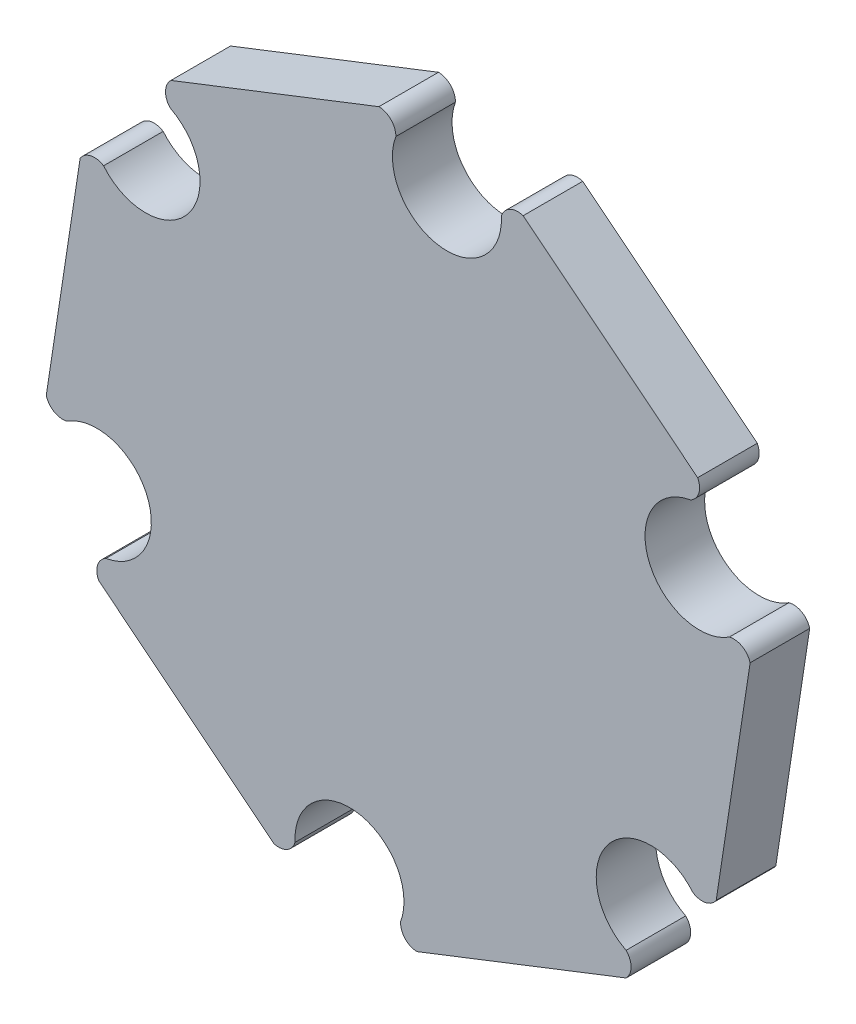
SolidWorks part; units mm, degrees
material "1060 slitina"
ref_plane "Přední rovina" through (0, 0, 0) normal (0, 0, 1) x (1, 0, 0)
ref_plane "Horní rovina" through (0, 0, 0) normal (0, 1, 0) x (1, 0, 0)
ref_plane "Pravá rovina" through (0, 0, 0) normal (1, 0, 0) x (0, 0, -1)
sketch "Skica1" plane through (0, 0, 0) normal (0, 0, 1) x (1, 0, 0)
  line L1 (-5.3857, 0.2391) -> (-4.3897, 6.7784)
  line L2 (-5.9299, 10.7161) -> (-11.0543, 14.8156)
  line L3 (-21.3984, 13.0839) -> (-15.2896, 15.4706)
  line L4 (-24.0633, 9.7716) -> (-25.0577, 3.243)
  line L5 (-23.518, -0.6978) -> (-18.3711, -4.8153)
  line L6 (-14.1786, -5.4602) -> (-8.0304, -3.0582)
  line L12 (-12.994, 16.3674) -> (-23.6955, 12.1864) [skipped]
  line L23 (-6.4189, 0.3965) -> (-6.3928, 0.3925)
  arc A2 (-14.7931, 14.9589) -> (-11.6959, 14.4872) centre (-13.2935, 14.4008) ccw
  arc A3 (-6.1418, 10.0439) -> (-5.0017, 7.1258) centre (-5.8753, 8.4662) ccw
  arc A4 (-23.3752, 9.9241) -> (-21.4181, 12.3705) centre (-22.1422, 10.9437) ccw
  arc A5 (-6.0709, 0.0971) -> (-8.0323, -2.3546) centre (-7.3057, -0.9255) ccw
  arc A6 (-14.6548, -4.9406) -> (-17.752, -4.4689) centre (-16.1543, -4.3826) ccw
  arc A7 (-23.3061, -0.0256) -> (-24.4462, 2.8925) centre (-23.5726, 1.552) ccw
  arc A8 (-11.6959, 14.4872) -> (-11.0543, 14.8156) centre (-11.2109, 14.3306) cw
  arc A9 (-5.9299, 10.7161) -> (-6.1418, 10.0439) centre (-6.3719, 10.4859) cw
  arc A10 (-5.0017, 7.1258) -> (-4.3897, 6.7784) centre (-4.8699, 6.6451) cw
  arc A11 (-15.2896, 15.4706) -> (-14.7931, 14.9589) centre (-15.2972, 14.9665) cw
  arc A12 (-21.4181, 12.3705) -> (-21.3984, 13.0839) centre (-21.0516, 12.7173) cw
  arc A13 (-24.0633, 9.7716) -> (-23.3752, 9.9241) centre (-23.643, 9.5038) cw
  arc A14 (-5.3857, 0.2391) -> (-6.0709, 0.0971) centre (-5.7993, 0.5107) cw
  arc A15 (-8.0323, -2.3546) -> (-8.0304, -3.0582) centre (-8.3831, -2.7073) cw
  arc A16 (-14.1786, -5.4602) -> (-14.6548, -4.9406) centre (-14.1569, -4.9623) cw
  arc A17 (-17.752, -4.4689) -> (-18.3711, -4.8153) centre (-18.2348, -4.3326) cw
  arc A18 (-24.4462, 2.8925) -> (-25.0577, 3.243) centre (-24.5767, 3.3735) cw
  arc A19 (-23.518, -0.6978) -> (-23.3061, -0.0256) centre (-23.076, -0.4677) cw
extrude "Přidat vysunutím1" add sketch "Skica1" along normal blind 1.75 contours A19 L5 A17 A6 A16 L6 A15 A5 A14 L1 A10 A3 A9 L2 A8 A2 A11 L3 A12 A4 A13 L4 A18 A7
ref_plane "Rovina1" through (0, 0, 1.75) normal (0, 0, 1) x (1, 0, 0)
sketch "Skica2" plane through (0, 0, 1.75) normal (0, 0, 1) x (1, 0, 0)
  line L0 (-20.8928, 9.9442) -> (-8.5576, 0.0761) construction
  line L1 (-8.4921, 12.7659) -> (-20.9446, -2.7566) construction
  line L2 (-5.9299, 10.7161) -> (-11.0543, 14.8156) construction
  line L3 (-23.518, -0.6978) -> (-18.3711, -4.8153) construction
  line L4 (-18.344, 14.2772) -> (-11.1045, -4.2592) construction
  line L5 (-21.3984, 13.0839) -> (-15.2896, 15.4706) construction
  line L6 (-14.1786, -5.4602) -> (-8.0304, -3.0582) construction
  line L7 (-13.5345, 12.8191) -> (-15.9134, -2.8008) construction
  arc A0 (-23.3752, 9.9241) -> (-21.4181, 12.3705) centre (-22.1422, 10.9437) ccw construction
  arc A1 (-6.0709, 0.0971) -> (-8.0323, -2.3546) centre (-7.3057, -0.9255) ccw construction
  arc A2 (-14.7931, 14.9589) -> (-11.6959, 14.4872) centre (-13.2935, 14.4008) ccw construction
  arc A3 (-14.6548, -4.9406) -> (-17.752, -4.4689) centre (-16.1543, -4.3826) ccw construction
  point P28 (-14.7252, 5.0101)
ref_plane "Rovina2" through (0, 0, 0) normal (0, 0, -1) x (-1, 0, 0)
sketch "Skica3" plane through (0, 0, 0) normal (0, 0, -1) x (-1, 0, 0)
  line L0 (18.344, 14.2772) -> (11.1045, -4.2592) construction
  line L1 (21.3984, 13.0839) -> (15.2896, 15.4706) construction
  line L2 (14.1786, -5.4602) -> (8.0304, -3.0582) construction
  line L3 (24.5605, 6.5073) -> (4.8877, 3.5088) construction
  line L4 (24.0633, 9.7716) -> (25.0577, 3.243) construction
  line L5 (5.3857, 0.2391) -> (4.3897, 6.7784) construction
  point P12 (14.7242, 5.009)
